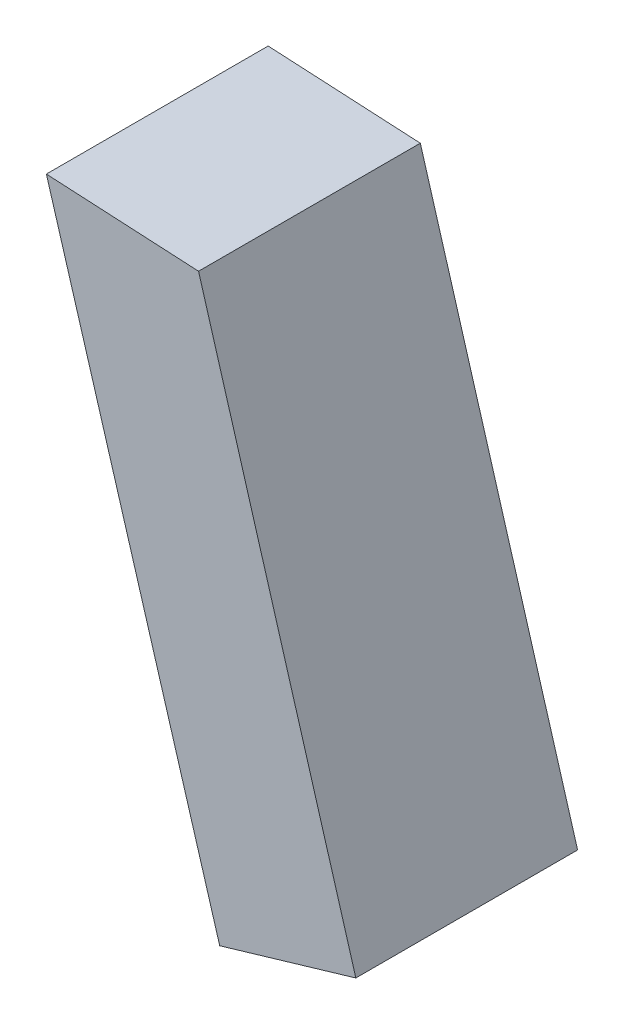
SolidWorks part; units mm, degrees
ref_plane "Alzado" through (0, 0, 0) normal (0, 0, 1) x (1, 0, 0)
ref_plane "Planta" through (0, 0, 0) normal (0, 1, 0) x (1, 0, 0)
ref_plane "Vista lateral" through (0, 0, 0) normal (1, 0, 0) x (0, 0, -1)
ref_plane "Plane1" through (0, 0, -0.375) normal (0, 0, -1) x (-1, 0, 0)
sketch "Sketch1" plane through (0, 0, -0.375) normal (0, 0, -1) x (-1, 0, 0)
  line L0 (-1.6819, 0.9556) -> (-2.0366, -0.247)
  line L1 (-2.0366, -0.247) -> (-1.7297, -0.3375)
  line L2 (-1.7297, -0.3375) -> (-1.3389, 0.9739)
  line L3 (-1.3389, 0.9739) -> (-1.6819, 0.9556)
  dimension "D1" = 0.3069
  dimension "D2" = 0.3547
  dimension "D3" = 0.6977
  dimension "D4" = 0.0905
  dimension "D5" = 1.2931
  dimension "D6" = 1.3114
extrude "Boss-Extrude1" add sketch "Sketch1" against normal blind 0.5
